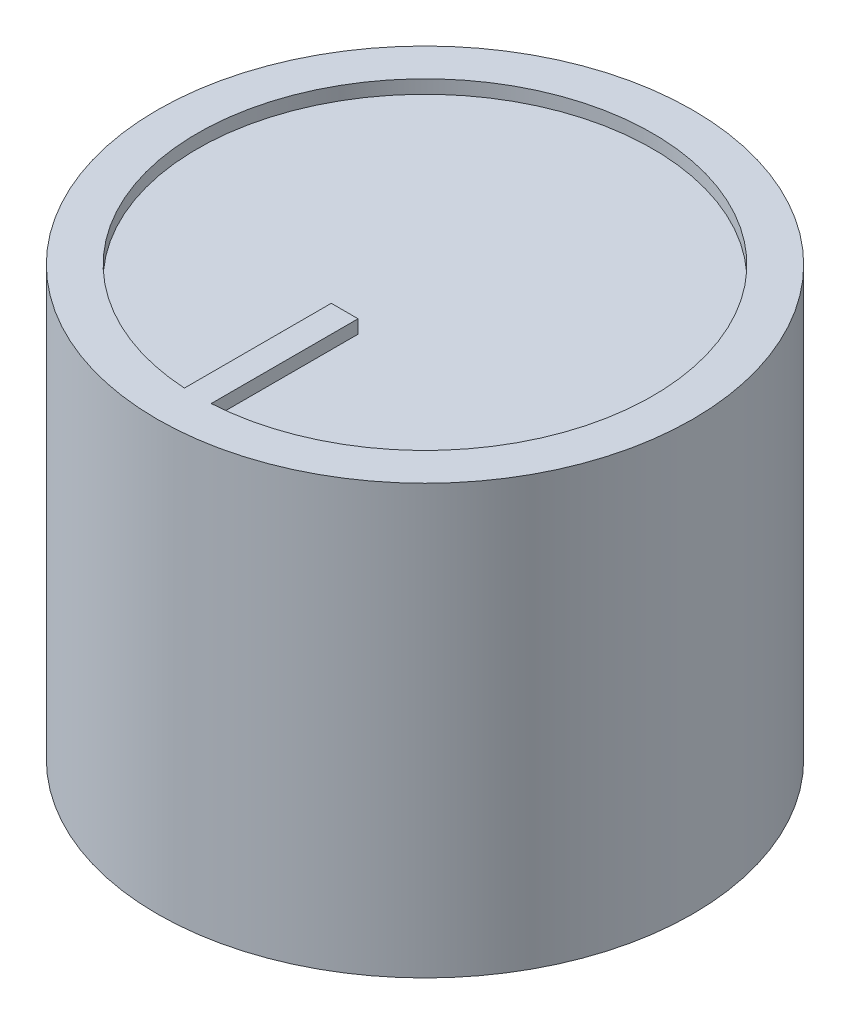
SolidWorks part; units mm, degrees
ref_plane "Спереди" through (0, 0, 0) normal (0, 0, 1) x (1, 0, 0)
ref_plane "Сверху" through (0, 0, 0) normal (0, 1, 0) x (1, 0, 0)
ref_plane "Справа" through (0, 0, 0) normal (1, 0, 0) x (0, 0, -1)
sketch "Эскиз1" plane through (0, 0, 0) normal (1, 0, 0) x (0, 0, -1)
  line L0 (0, 0) -> (-3, 0)
  line L1 (-3, 0) -> (-3, -9.5)
  line L2 (-3, -9.5) -> (-4.5, -9.5)
  line L3 (-4.5, -9.5) -> (-4.5, -2)
  line L4 (-4.5, -2) -> (-6, -2)
  line L5 (-6, -2) -> (-6, -13)
  line L6 (-6, -13) -> (-10, -13)
  line L7 (-10, -13) -> (-10, 3)
  line L8 (-10, 3) -> (-8.5, 3)
  line L9 (-8.5, 3) -> (-8.5, 2.5)
  line L10 (-8.5, 2.5) -> (0, 2.5)
  line L11 (0, 2.5) -> (0, 0) construction
  line L12 (0, 0) -> (0, 2.5)
  point P15 (-1.5, 0)
  dimension "D1" = 6
  dimension "D2" = 3.5
  dimension "D3" = 13
  dimension "D4" = 16
  dimension "D5" = 0.5
  dimension "D6" = 12
  dimension "D7" = 20
  dimension "D8" = 1.5
  dimension "D9" = 2
revolve "Повернуть1" add sketch "Эскиз1" angle 360 about L11
sketch "Эскиз2" plane through (0, 2.5, 0) normal (0, 1, 0) x (1, 0, 0)
  line L0 (0, 0) -> (0, -3) construction
  line L1 (-0.5, -3) -> (0.5, -3)
  line L2 (-0.5, -3) -> (-0.5, -8.5)
  line L3 (-0.5, -8.5) -> (0.5, -8.5)
  line L4 (0.5, -3) -> (0.5, -8.5)
  line L5 (0, -3) -> (0, -4.5) construction
  line L6 (0, -3) -> (0, -4.5) construction
  line L7 (0, -10) -> (0, -8.5) construction
  line L8 (0, -10) -> (0, -8.5) construction
  point P4 (0, -3)
  dimension "D1" = 1
extrude "Бобышка-Вытянуть1" add sketch "Эскиз2" along normal up to surface (0.5 mm away) up to face at (0, 3, 10)
